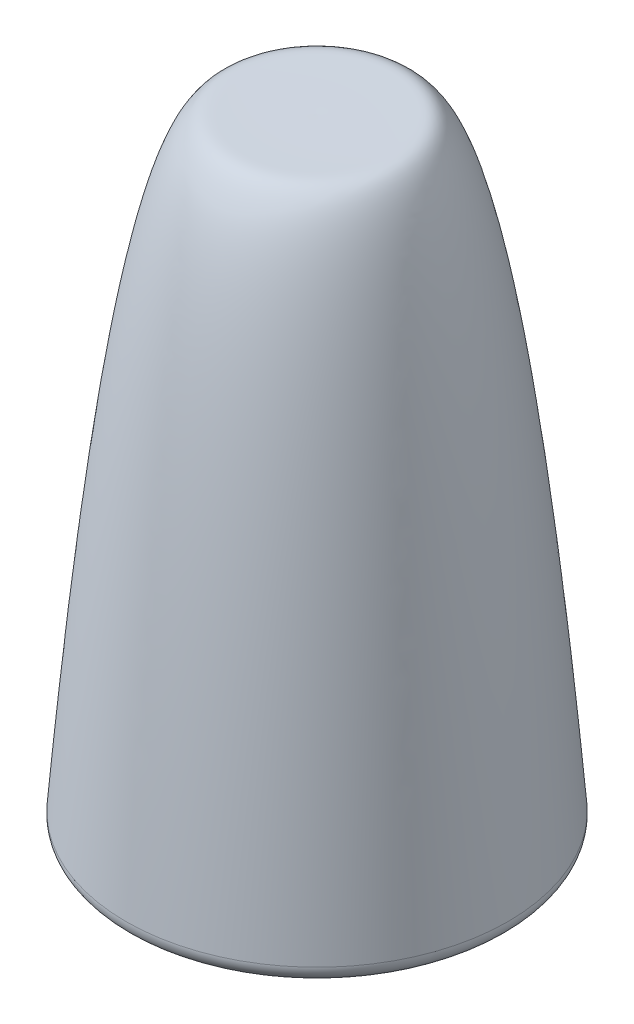
SolidWorks part; units mm, degrees
material "BUTYL"
ref_plane "Plano frontal" through (0, 0, 0) normal (0, 0, 1) x (1, 0, 0)
ref_plane "Plano superior" through (0, 0, 0) normal (0, 1, 0) x (1, 0, 0)
ref_plane "Plano direito" through (0, 0, 0) normal (1, 0, 0) x (0, 0, -1)
sketch "Esboço1" plane through (0, 0, 0) normal (0, 0, 1) x (1, 0, 0)
  line L0 (0, 0) -> (6.2, 0)
  line L1 (0, 0) -> (8.0091, 0) construction
  line L2 (0, 20) -> (0, 0)
  spline S0 degree 3 poles (0, 20) (0.4324, 20.0048) (1.9674, 19.9986) (3.6652, 20.0633) (5.0722, 14.4719) (6.2, 0) knots 0 0 0 0 0.288601 0.388601 1 1 1 1
  point P7 (6.2, 0)
  point P10 (2.8, 20)
  dimension "D1" = 20
  dimension "D2" = 6.2
  dimension "D3" = 2.8
revolve "Revolução1" add sketch "Esboço1" angle 360 about L2
fillet "Filete1" radius 0.5 1 edges at (-6.2, 0, 0)
sketch "Esboço2" plane through (0, 0, 0) normal (0, -1, 0) x (1, 0, 0)
  circle A0 centre (0, 0) radius 1.5
extrude "Corte-extrusão1" cut sketch "Esboço2" against normal blind 5
